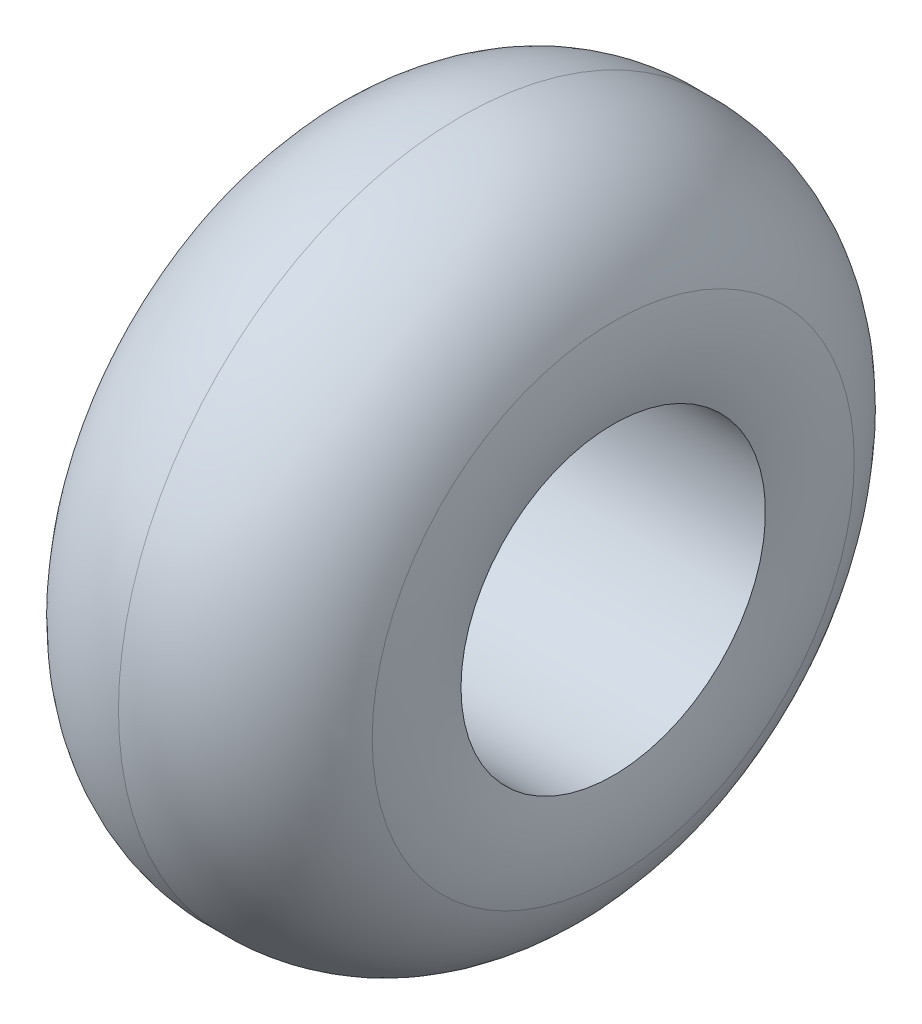
SolidWorks part; units mm, degrees
ref_plane "Front Plane" through (0, 0, 0) normal (0, 0, 1) x (1, 0, 0)
ref_plane "Top Plane" through (0, 0, 0) normal (0, 1, 0) x (1, 0, 0)
ref_plane "Right Plane" through (0, 0, 0) normal (1, 0, 0) x (0, 0, -1)
sketch "Sketch1" plane through (0, 0, 0) normal (0, 0, 1) x (1, 0, 0)
  line L0 (0, 0) -> (200.5515, 0) construction
  line L1 (-76.2, 76.2) -> (76.2, 76.2)
  line L2 (0, 76.2) -> (0, 171.45)
  arc A6 (0, 171.45) -> (76.2, 120.65) centre (4.3148, 95.3723) cw
  arc A7 (76.2, 120.65) -> (76.2, 76.2) centre (-5.8711, 98.425) cw
  arc A8 (0, 171.45) -> (-76.2, 120.65) centre (-4.3148, 95.3723) ccw
  arc A9 (-76.2, 120.65) -> (-76.2, 76.2) centre (-16.6509, 98.425) ccw
  dimension "D2" = 152.4
  dimension "D5" = 63.5614
  dimension "D6" = 85.0271
  dimension "D7" = 76.2
  dimension "D8" = 76.2
  dimension "D9" = 50.8
  dimension "D1" = 76.2
  dimension "D3" = 76.2
  dimension "D4" = 95.25
  dimension "D10" = 50.8
  dimension "D11" = 76.2
  dimension "D12" = 76.2
  dimension "D13" = 44.45
revolve "Revolve1" add sketch "Sketch1" angle 360 about L0
